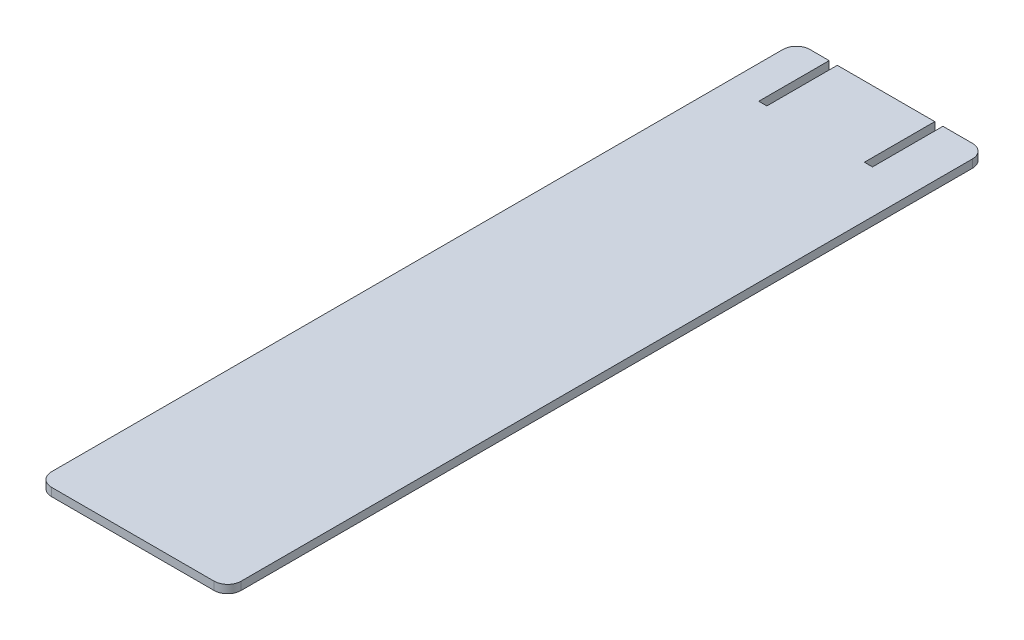
SolidWorks part; units mm, degrees
ref_plane "Front Plane" through (0, 0, 0) normal (0, 0, 1) x (1, 0, 0)
ref_plane "Top Plane" through (0, 0, 0) normal (0, 1, 0) x (1, 0, 0)
ref_plane "Right Plane" through (0, 0, 0) normal (1, 0, 0) x (0, 0, -1)
sketch "Sketch1" plane through (0, 0, 0) normal (0, 1, 0) x (1, 0, 0)
  line L1 (145.5807, 100.4887) -> (205.5807, 100.4887)
  line L2 (140.5807, 95.4887) -> (140.5807, -174.5113)
  line L3 (145.5807, -179.5113) -> (205.5807, -179.5113)
  line L4 (210.5807, 95.4887) -> (210.5807, -174.5113)
  arc A0 (205.5807, -179.5113) -> (210.5807, -174.5113) centre (205.5807, -174.5113) ccw
  arc A1 (140.5807, -174.5113) -> (145.5807, -179.5113) centre (145.5807, -174.5113) ccw
  arc A2 (145.5807, 100.4887) -> (140.5807, 95.4887) centre (145.5807, 95.4887) ccw
  arc A3 (205.5807, 100.4887) -> (210.5807, 95.4887) centre (205.5807, 95.4887) cw
  point P6 (210.5807, -179.5113)
  point P11 (140.5807, 100.4887)
  point P14 (210.5807, 100.4887)
  dimension "D3" = 5
  dimension "D1" = 280
  dimension "D2" = 70
extrude "Boss-Extrude1" add sketch "Sketch1" along normal blind 3
sketch "Sketch2" plane through (0, 3, 0) normal (0, 1, 0) x (1, 0, 0)
  line L0 (152.688, 100.4887) -> (155.688, 100.4887)
  line L1 (205.5807, 100.4887) -> (145.5807, 100.4887) construction
  line L2 (155.688, 100.4887) -> (155.688, 74.4887)
  line L3 (155.688, 74.4887) -> (152.688, 74.4888)
  line L4 (152.688, 74.4888) -> (152.688, 100.4887)
  line L5 (191.688, 100.4887) -> (194.688, 100.4887)
  line L6 (194.688, 100.4887) -> (194.688, 74.4887)
  line L7 (194.688, 74.4887) -> (191.688, 74.4887)
  line L8 (191.688, 74.4887) -> (191.688, 100.4887)
  dimension "D1" = 3
  dimension "D2" = 3
  dimension "D3" = 26
  dimension "D4" = 36
extrude "Cut-Extrude1" cut sketch "Sketch2" against normal through all
